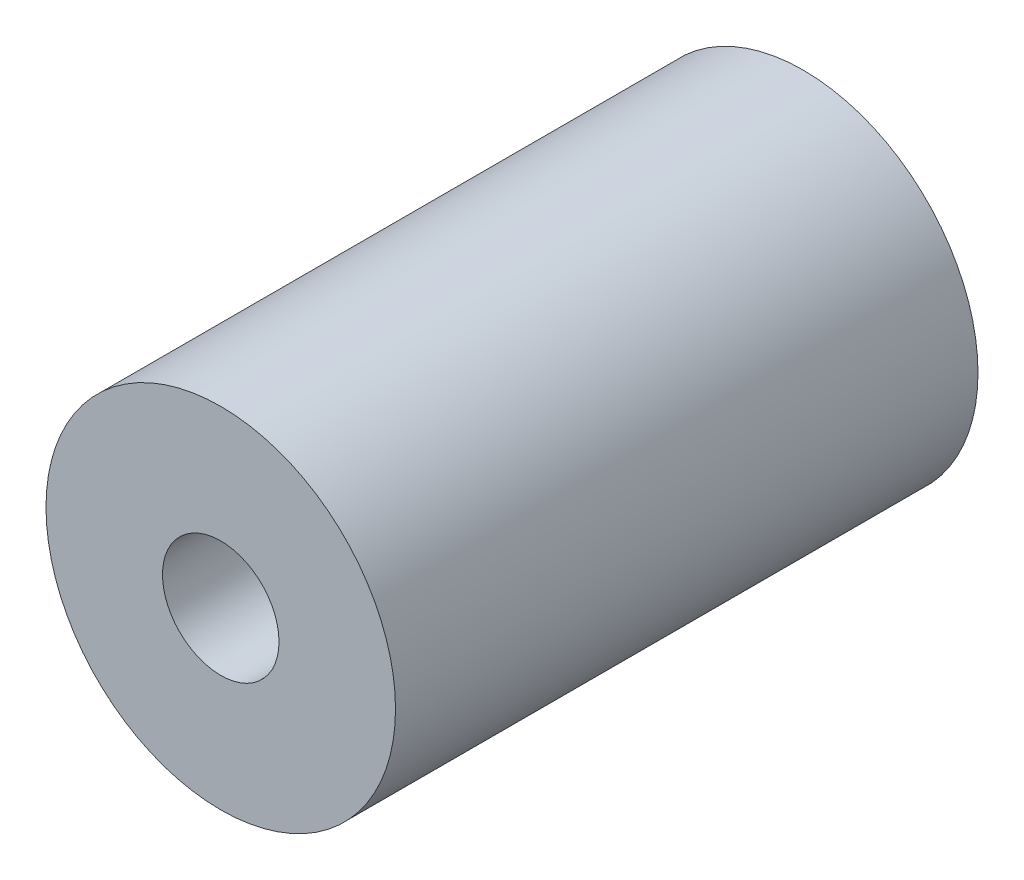
SolidWorks part; units mm, degrees
ref_plane "Спереди" through (0, 0, 0) normal (0, 0, 1) x (1, 0, 0)
ref_plane "Сверху" through (0, 0, 0) normal (0, 1, 0) x (1, 0, 0)
ref_plane "Справа" through (0, 0, 0) normal (1, 0, 0) x (0, 0, -1)
sketch "Эскиз1" plane through (0, 0, 0) normal (0, 0, 1) x (1, 0, 0)
  circle A0 centre (0, 0) radius 10
  circle A1 centre (0, 0) radius 30
  dimension "D1" = 60
extrude "Бобышка-Вытянуть1" add sketch "Эскиз1" along normal blind 100
